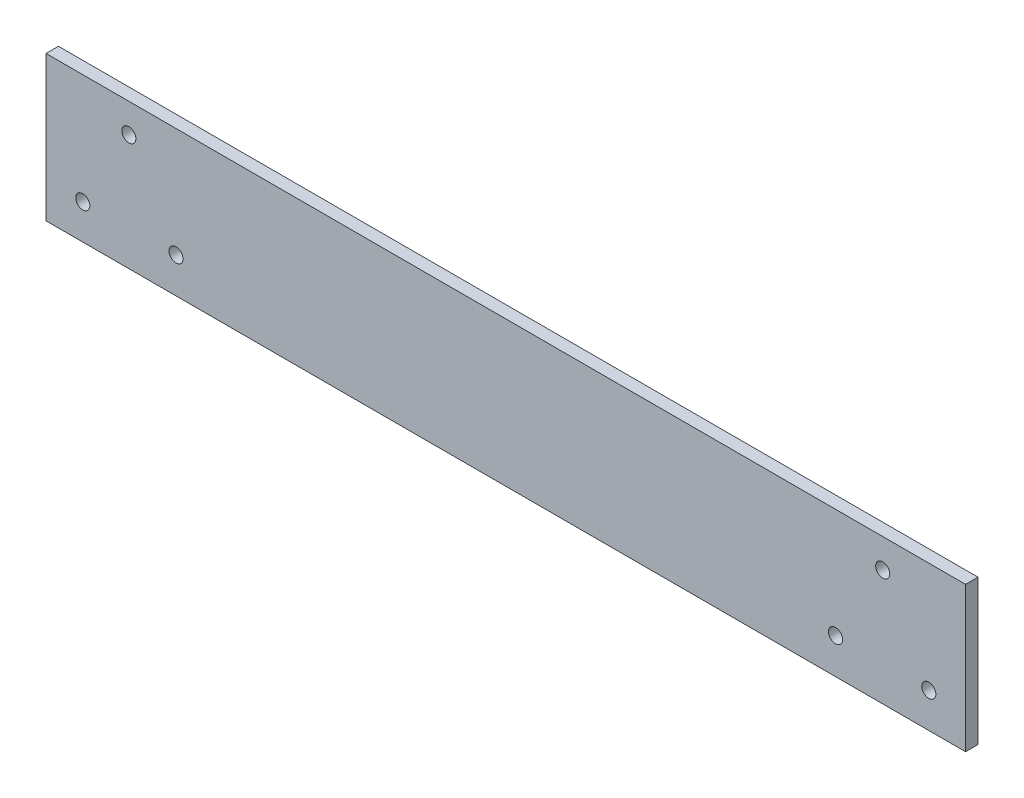
SolidWorks part; units mm, degrees
ref_plane "Plan de face" through (0, 0, 0) normal (0, 0, 1) x (1, 0, 0)
ref_plane "Plan de dessus" through (0, 0, 0) normal (0, 1, 0) x (1, 0, 0)
ref_plane "Plan de droite" through (0, 0, 0) normal (1, 0, 0) x (0, 0, -1)
sketch "Esquisse1" plane through (0, 0, 0) normal (0, 0, 1) x (1, 0, 0)
  line L0 (-35.3771, -9.3042) -> (-35.3771, 14.9761) construction
  line L1 (-55.3771, 10.6958) -> (166.6229, 10.6958)
  line L2 (-55.3771, 10.6958) -> (-55.3771, -24.3042)
  line L3 (-55.3771, -24.3042) -> (166.6229, -24.3042)
  line L4 (166.6229, 10.6958) -> (166.6229, -24.3042)
  line L5 (-55.3771, 10.6958) -> (166.6229, -24.3042) construction
  line L6 (-55.3771, -24.3042) -> (166.6229, 10.6958) construction
  line L7 (55.6229, -6.8042) -> (55.6229, 10.6958) construction
  circle A0 centre (-35.3771, 3.6958) radius 1.7
  circle A1 centre (-23.9784, -15.7231) radius 1.7
  circle A2 centre (-46.4951, -15.8852) radius 1.7
  circle A3 centre (135.2242, -15.7231) radius 1.7
  circle A4 centre (157.7409, -15.8852) radius 1.7
  circle A5 centre (146.6229, 3.6958) radius 1.7
  point P4 (-35.3771, -9.3042)
  dimension "D5" = 13
  dimension "D7" = 3
  dimension "D6" = 3.4
  dimension "D1" = 35
  dimension "D2" = 222
  dimension "D3" = 20
  dimension "D4" = 20
  dimension "D8" = 0
extrude "Boss.-Extru.1" add sketch "Esquisse1" along normal blind 3
